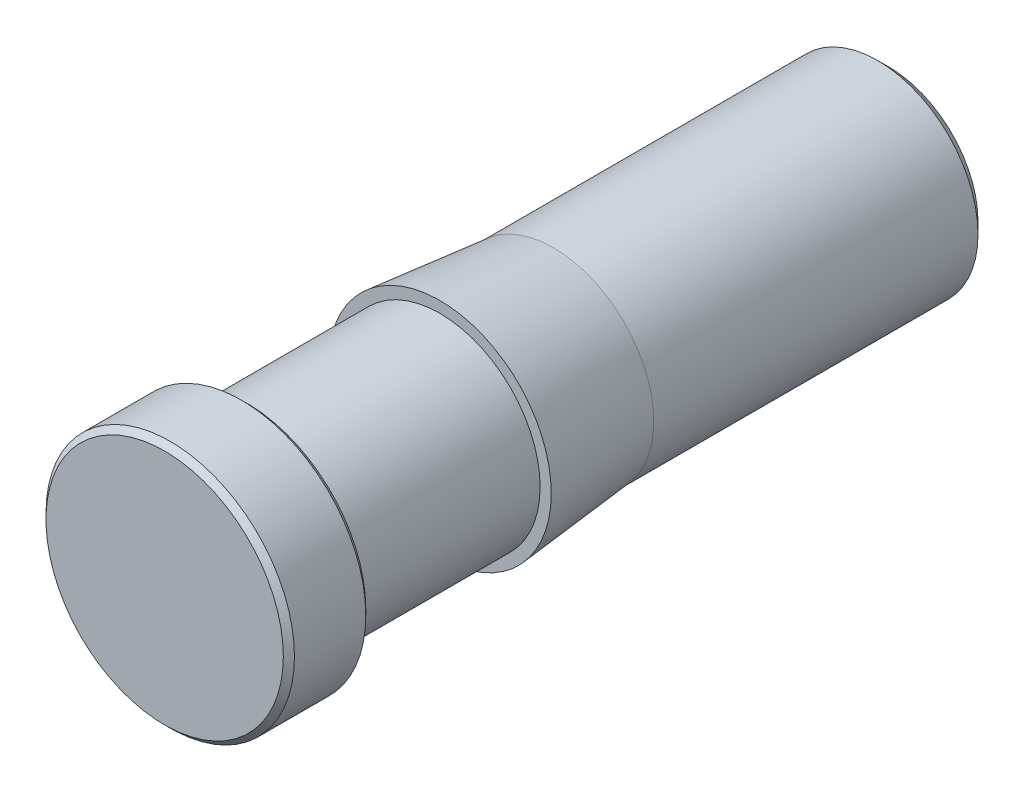
SolidWorks part; units mm, degrees
ref_plane "Plan de face" through (0, 0, 0) normal (0, 0, 1) x (1, 0, 0)
ref_plane "Plan de dessus" through (0, 0, 0) normal (0, 1, 0) x (1, 0, 0)
ref_plane "Plan de droite" through (0, 0, 0) normal (1, 0, 0) x (0, 0, -1)
sketch "Esquisse1" plane through (0, 0, 0) normal (0, 1, 0) x (1, 0, 0)
  line L0 (0.65, 5.17) -> (0, 4.7947)
  line L1 (0, 4.7947) -> (0, 0)
  line L2 (0, 0) -> (1.065, 0)
  line L3 (1.065, 0) -> (1.115, 0.05)
  line L4 (1.115, 0.05) -> (1.115, 0.69)
  line L5 (1.115, 0.69) -> (1.065, 0.74)
  line L6 (1.065, 0.74) -> (0.9, 0.74)
  line L7 (0.9, 0.74) -> (0.9, 2.47)
  line L8 (0.9, 2.47) -> (1, 2.47)
  line L9 (1, 2.47) -> (0.9, 3.49)
  line L10 (0.9, 3.49) -> (0.9, 6.4)
  line L11 (0.9, 6.4) -> (0.8, 6.5)
  line L12 (0.8, 6.5) -> (0.7, 6.5)
  line L13 (0.7, 6.5) -> (0.65, 6.45)
  line L14 (0.65, 6.45) -> (0.65, 5.17)
  line L15 (0, 6.5) -> (0, 0) construction
revolve "Révolution1" add sketch "Esquisse1" angle 360 about L15
